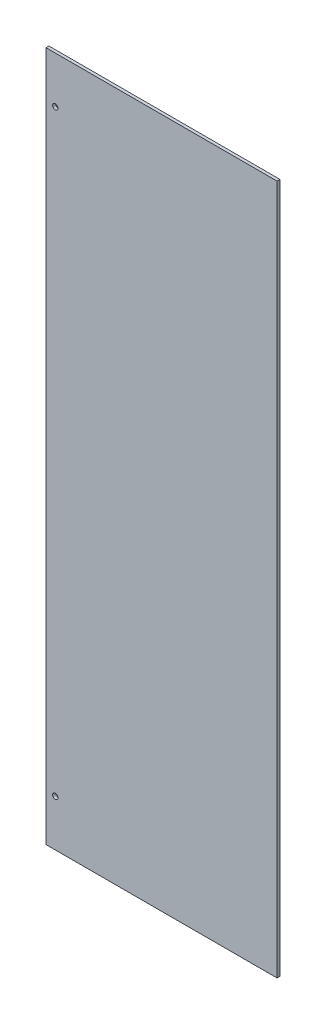
SolidWorks part; units mm, degrees
material "6061 Alloy"
ref_plane "Front" through (0, 0, 0) normal (0, 0, 1) x (1, 0, 0)
ref_plane "Top" through (0, 0, 0) normal (0, 1, 0) x (1, 0, 0)
ref_plane "Right" through (0, 0, 0) normal (1, 0, 0) x (0, 0, -1)
sketch "Sketch1" plane through (0, 0, 0) normal (0, 0, 1) x (1, 0, 0)
  line L1 (0, 0) -> (126.0475, 0)
  line L2 (0, 0) -> (0, 376.555)
  line L3 (0, 376.555) -> (126.0475, 376.555)
  line L4 (126.0475, 0) -> (126.0475, 376.555)
  dimension "D1" = 376.555
  dimension "D2" = 126.0475
extrude "Boss-Extrude1" add sketch "Sketch1" along normal blind 1.5875
sketch "Sketch2" plane through (0, 0, 1.5875) normal (0, 0, 1) x (1, 0, 0)
  line L0 (0, 376.555) -> (0, 0) construction
  line L1 (126.0475, 376.555) -> (0, 376.555) construction
  circle A0 centre (5.08, 351.155) radius 1.4605
  dimension "D3" = 2.921
  dimension "D1" = 5.08
  dimension "D2" = 25.4
extrude "Cut-Extrude1" cut sketch "Sketch2" against normal blind 6.35
pattern_linear "LPattern1" count 2 spacing 325.755 along (0, -1, 0) of "Cut-Extrude1"
